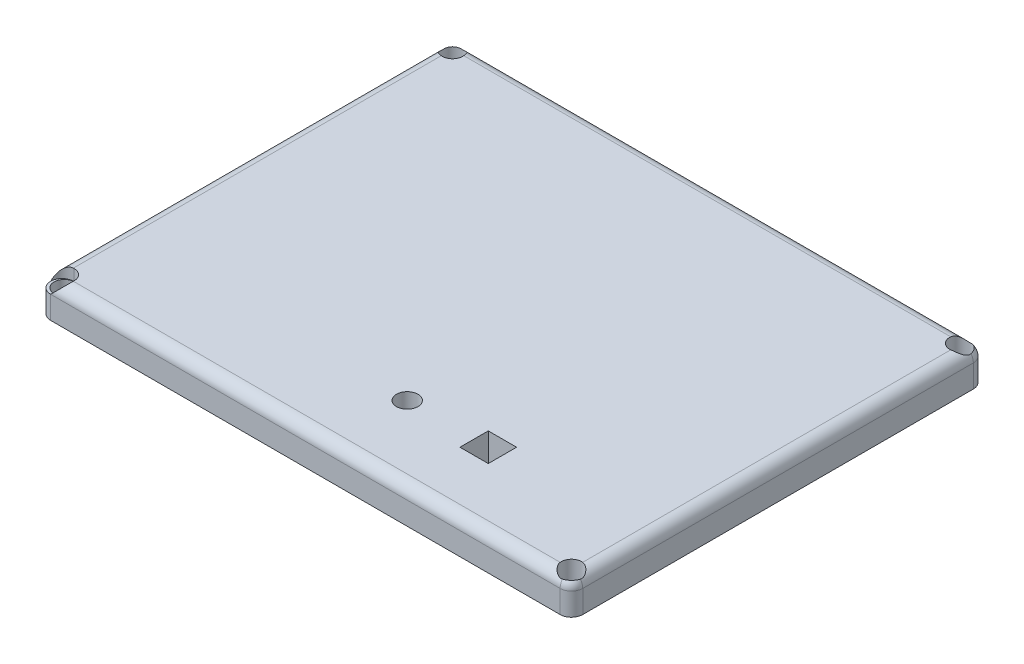
SolidWorks part; units mm, degrees
ref_plane "Front Plane" through (0, 0, 0) normal (0, 0, 1) x (1, 0, 0)
ref_plane "Top Plane" through (0, 0, 0) normal (0, 1, 0) x (1, 0, 0)
ref_plane "Right Plane" through (0, 0, 0) normal (1, 0, 0) x (0, 0, -1)
sketch "Sketch1" plane through (0, 0, 0) normal (0, 1, 0) x (1, 0, 0)
  line L1 (-59.69, -46.355) -> (59.69, -46.355)
  line L2 (-59.69, -46.355) -> (-59.69, 46.355)
  line L3 (-59.69, 46.355) -> (59.69, 46.355)
  line L4 (59.69, -46.355) -> (59.69, 46.355)
  line L5 (-59.69, -46.355) -> (59.69, 46.355) construction
  line L6 (-59.69, 46.355) -> (59.69, -46.355) construction
  point P0 (0, 0)
  dimension "D1" = 119.38
  dimension "D2" = 92.71
extrude "Boss-Extrude1" add sketch "Sketch1" along normal blind 7.62
fillet "Fillet1" radius 2.54 8 edges at (-59.69, 3.81, -46.355) (0, 7.62, -46.355) (-59.69, 7.62, 0) (0, 7.62, 46.355) (59.69, 7.62, 0) (59.69, 3.81, -46.355) (59.69, 3.81, 46.355) (-59.69, 3.81, 46.355)
sketch "Sketch3" plane through (0, 0, 0) normal (0, -1, 0) x (1, 0, 0)
  circle A0 centre (6.0087, 29.5186) radius 2.413
  dimension "D1" = 4.826
extrude "Cut-Extrude1" cut sketch "Sketch3" against normal blind 8.128
sketch "Sketch4" plane through (0, 0, 0) normal (0, -1, 0) x (1, 0, 0)
  line L0 (21.0183, 32.6933) -> (27.3683, 26.3433) construction
  line L1 (21.0183, 32.6933) -> (27.3683, 32.6933)
  line L2 (21.0183, 32.6933) -> (21.0183, 26.3433)
  line L3 (21.0183, 26.3433) -> (27.3683, 26.3433)
  line L4 (27.3683, 32.6933) -> (27.3683, 26.3433)
  point P6 (24.1933, 29.5183)
  point P7 (24.1933, 29.5183)
  dimension "D1" = 6.35
extrude "Cut-Extrude2" cut sketch "Sketch4" against normal up to surface (7.62 mm away) up to face at (6.0087, 7.62, 27.1056)
sketch "Sketch5" plane through (0, 7.62, 0) normal (0, 1, 0) x (1, 0, 0)
  circle A0 centre (-57.15, -43.815) radius 2.54
extrude "Cut-Extrude3" cut sketch "Sketch5" against normal blind 2.54
sketch "Sketch6" plane through (0, 0, 0) normal (0, -1, 0) x (-1, 0, 0)
  line L0 (-59.69, -43.815) -> (-59.69, 43.815) construction
  line L1 (54.864, -41.529) -> (-54.864, -41.529)
  line L2 (54.864, -41.529) -> (54.864, 41.529)
  line L3 (54.864, 41.529) -> (-54.864, 41.529)
  line L4 (-54.864, -41.529) -> (-54.864, 41.529)
  line L5 (54.864, -41.529) -> (-54.864, 41.529) construction
  line L6 (54.864, 41.529) -> (-54.864, -41.529) construction
  line L8 (57.15, -46.355) -> (-57.15, -46.355) construction
  line L9 (-57.15, 46.355) -> (57.15, 46.355) construction
  line L10 (59.69, 43.815) -> (59.69, -43.815) construction
  line L11 (52.324, -38.989) -> (-52.324, -38.989)
  line L12 (52.324, -38.989) -> (52.324, 38.989)
  line L13 (52.324, 38.989) -> (-52.324, 38.989)
  line L14 (-52.324, -38.989) -> (-52.324, 38.989)
  line L15 (52.324, -38.989) -> (-52.324, 38.989) construction
  line L16 (52.324, 38.989) -> (-52.324, -38.989) construction
  point P0 (0, 0)
  point P13 (0, 0)
  dimension "D1" = 4.826
  dimension "D2" = 4.826
  dimension "D3" = 4.826
  dimension "D4" = 4.826
  dimension "D5" = 2.54
  dimension "D6" = 2.54
extrude "Boss-Extrude2" add sketch "Sketch6" along normal blind 2.54
sketch "Sketch8" plane through (0, 0, 0) normal (0, -1, 0) x (1, 0, 0)
  line L0 (59.69, 43.815) -> (59.69, -43.815) construction
  line L1 (-57.15, 46.355) -> (57.15, 46.355) construction
  circle A0 centre (56.896, 43.561) radius 2.286
  dimension "D1" = 4.572
  dimension "D2" = 2.794
  dimension "D3" = 2.794
extrude "Cut-Extrude4" cut sketch "Sketch8" against normal through all
sketch "Sketch9" plane through (0, 0, 0) normal (0, -1, 0) x (-1, 0, 0)
  line L0 (-59.69, -43.815) -> (-59.69, 43.815) construction
  line L1 (-57.15, 46.355) -> (57.15, 46.355) construction
  circle A0 centre (-56.896, 43.561) radius 2.286
  dimension "D1" = 4.572
  dimension "D2" = 2.794
  dimension "D3" = 2.794
extrude "Cut-Extrude5" cut sketch "Sketch9" against normal through all
sketch "Sketch11" plane through (0, 0, 0) normal (0, -1, 0) x (1, 0, 0)
  line L0 (57.15, -46.355) -> (-57.15, -46.355) construction
  line L1 (-59.69, -43.815) -> (-59.69, 43.815) construction
  circle A0 centre (-56.896, -43.561) radius 2.286
  dimension "D1" = 4.572
  dimension "D2" = 2.794
  dimension "D3" = 2.794
extrude "Cut-Extrude6" cut sketch "Sketch11" against normal through all
sketch "Sketch12" plane through (0, 0, 0) normal (0, -1, 0) x (1, 0, 0)
  line L0 (-59.69, -43.815) -> (-59.69, 43.815) construction
  line L1 (-57.15, 46.355) -> (57.15, 46.355) construction
  circle A0 centre (-56.896, 43.561) radius 2.286
  point P2 (0, 0)
  dimension "D1" = 4.572
  dimension "D2" = 2.794
  dimension "D3" = 2.794
extrude "Cut-Extrude7" cut sketch "Sketch12" against normal through all
